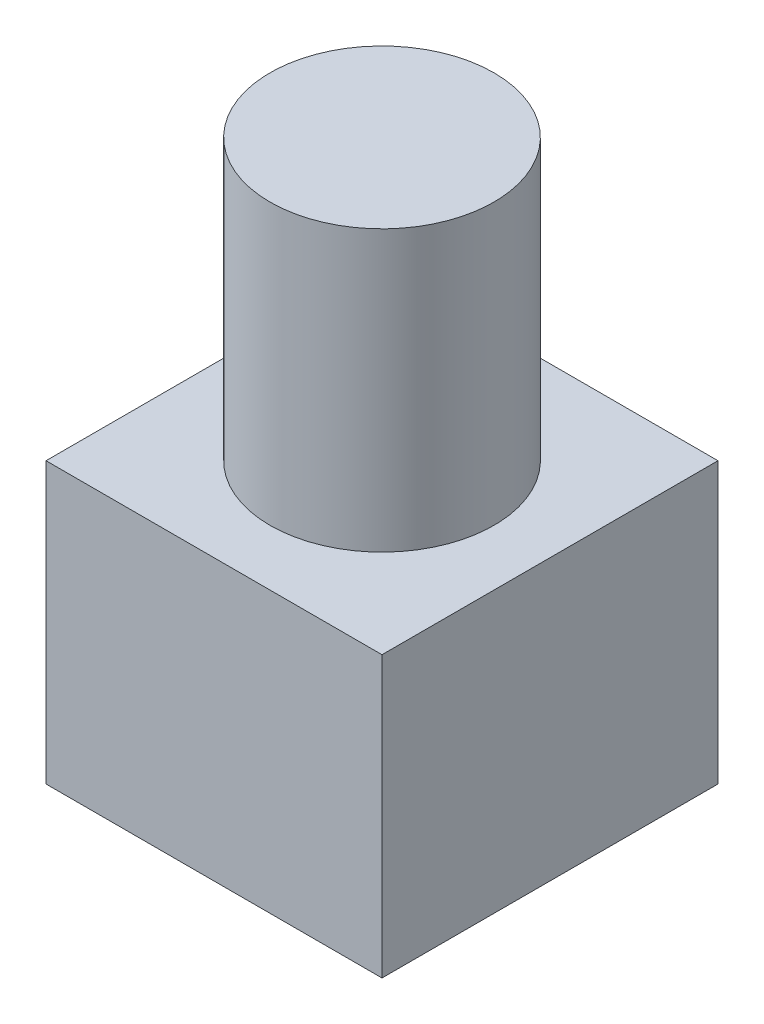
SolidWorks part; units mm, degrees
ref_plane "Front Plane" through (0, 0, 0) normal (0, 0, 1) x (1, 0, 0)
ref_plane "Top Plane" through (0, 0, 0) normal (0, 1, 0) x (1, 0, 0)
ref_plane "Right Plane" through (0, 0, 0) normal (1, 0, 0) x (0, 0, -1)
sketch "Sketch1" plane through (0, 0, 0) normal (0, 1, 0) x (1, 0, 0)
  line L1 (0, 0) -> (6, 0)
  line L2 (0, 0) -> (0, 6)
  line L3 (0, 6) -> (6, 6)
  line L4 (6, 0) -> (6, 6)
  dimension "D1" = 6
  dimension "D2" = 6
extrude "Boss-Extrude1" add sketch "Sketch1" along normal blind 5 contours L1 L4 L3 L2
sketch "Sketch2" plane through (0, 5, 0) normal (0, 1, 0) x (1, 0, 0)
  line L0 (0, 0) -> (0, 6) construction
  circle A0 centre (3, 3) radius 2
  dimension "D1" = 4
  dimension "D2" = 3
  dimension "D3" = 3
extrude "Boss-Extrude2" add sketch "Sketch2" along normal blind 5
